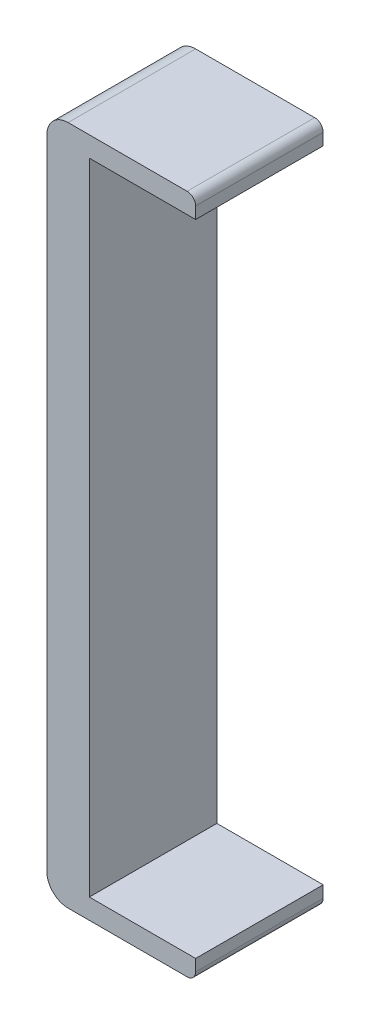
SolidWorks part; units mm, degrees
ref_plane "Front Plane" through (0, 0, 0) normal (0, 0, 1) x (1, 0, 0)
ref_plane "Top Plane" through (0, 0, 0) normal (0, 1, 0) x (1, 0, 0)
ref_plane "Right Plane" through (0, 0, 0) normal (1, 0, 0) x (0, 0, -1)
sketch "Sketch1" plane through (0, 0, 0) normal (0, 0, 1) x (1, 0, 0)
  line L0 (-17.5, 74.9999) -> (-17.5, -74.9999)
  line L1 (-12.5, -79.9999) -> (15.5, -79.9999)
  line L2 (17.5, -77.9999) -> (17.5, -75.2499)
  line L3 (17.5, -75.2499) -> (-7.5, -75.2499)
  line L4 (-7.5, -75.2499) -> (-7.5, 75.2501)
  line L5 (-7.5, 75.2501) -> (17.5, 75.2501)
  line L6 (17.5, 75.2501) -> (17.5, 77.9999)
  line L7 (15.5, 79.9999) -> (-12.5, 79.9999)
  arc A0 (-17.5, -74.9999) -> (-12.5, -79.9999) centre (-12.5, -74.9999) ccw
  arc A1 (15.5, -79.9999) -> (17.5, -77.9999) centre (15.5, -77.9999) ccw
  arc A2 (17.5, 77.9999) -> (15.5, 79.9999) centre (15.5, 77.9999) ccw
  arc A3 (-12.5, 79.9999) -> (-17.5, 74.9999) centre (-12.5, 74.9999) ccw
extrude "Boss-Extrude1" add sketch "Sketch1" along normal blind 30
